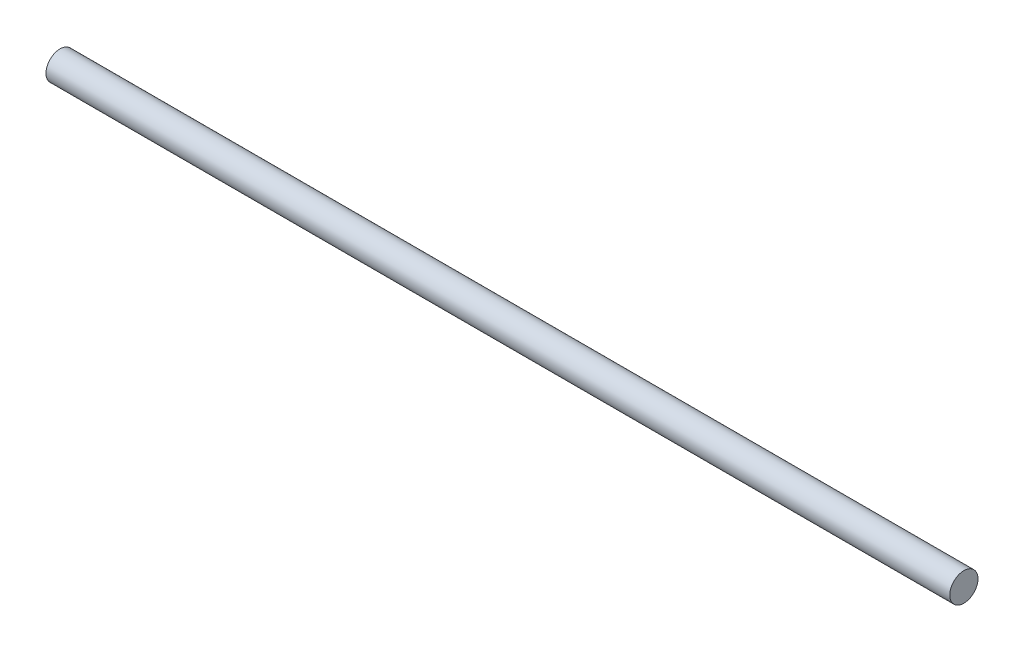
SolidWorks part; units mm, degrees
ref_plane "Front Plane" through (0, 0, 0) normal (0, 0, 1) x (1, 0, 0)
ref_plane "Top Plane" through (0, 0, 0) normal (0, 1, 0) x (1, 0, 0)
ref_plane "Right Plane" through (0, 0, 0) normal (1, 0, 0) x (0, 0, -1)
sketch "Sketch1" plane through (0, 0, 0) normal (1, 0, 0) x (0, 0, -1)
  circle A0 centre (0, 0) radius 3.9688
  dimension "D1" = 7.9375
extrude "Boss-Extrude1" add sketch "Sketch1" along normal blind 254
